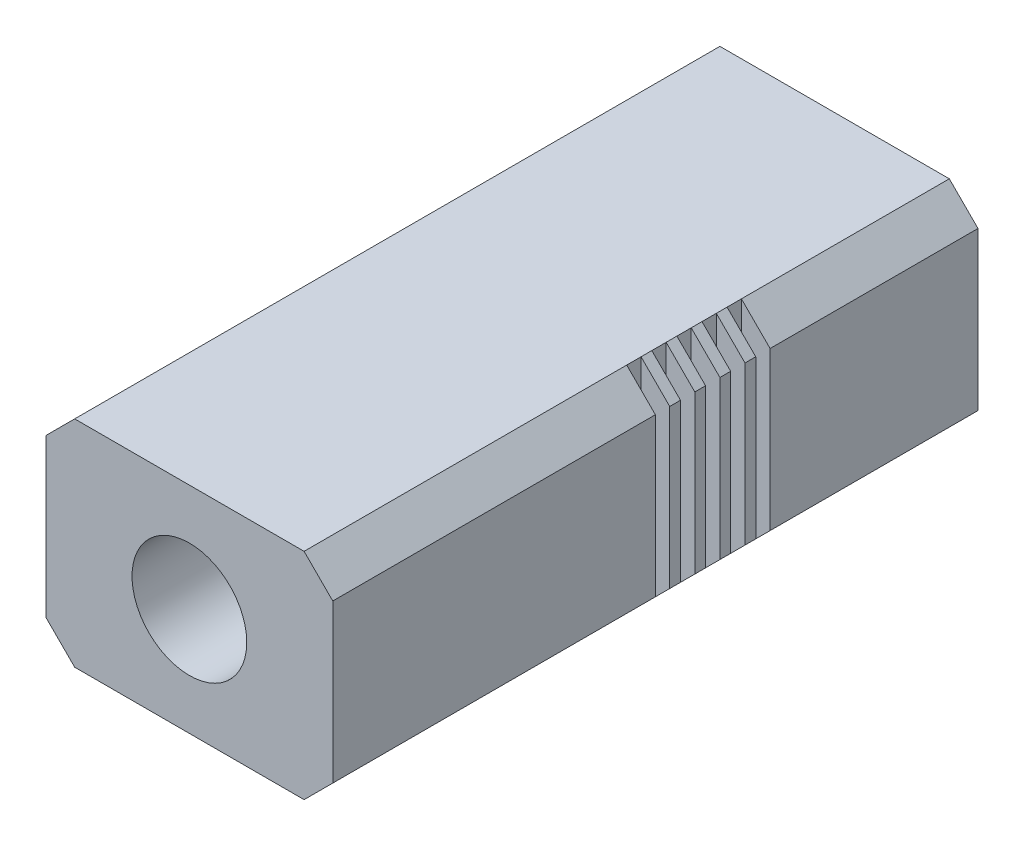
SolidWorks part; units mm, degrees
ref_plane "Front Plane" through (0, 0, 0) normal (0, 0, 1) x (1, 0, 0)
ref_plane "Top Plane" through (0, 0, 0) normal (0, 1, 0) x (1, 0, 0)
ref_plane "Right Plane" through (0, 0, 0) normal (1, 0, 0) x (0, 0, -1)
sketch "Sketch1" plane through (0, 0, 0) normal (0, 0, 1) x (1, 0, 0)
  line L0 (-10, 7.5) -> (-10, -7.5)
  line L1 (-10, 7.5) -> (10, 7.5)
  line L2 (-10, -7.5) -> (10, -7.5)
  line L3 (10, 7.5) -> (10, -7.5)
  line L4 (-10, 7.5) -> (10, -7.5) construction
  dimension "D1" = 20
  dimension "D2" = 15
extrude "Boss-Extrude1" add sketch "Sketch1" along normal blind 45
sketch "Sketch2" plane through (0, 0, 45) normal (0, 0, 1) x (1, 0, 0)
  circle A1 centre (0, 0) radius 4
  dimension "D3" = 8
extrude "Cut-Extrude1" cut sketch "Sketch2" against normal through all
chamfer "Chamfer1" distance 2 angle 45 4 edges at (-10, 7.5, 22.5) (-10, -7.5, 22.5) (10, -7.5, 22.5) (10, 7.5, 22.5)
sketch "Sketch4" plane through (0, -7.5, 0) normal (0, -1, 0) x (1, 0, 0)
  line L0 (-8, 45) -> (-8, 0) construction
  line L1 (-8, 14.5) -> (-10, 14.5)
  line L2 (-8, 14.5) -> (-8, 15.5)
  line L3 (-8, 15.5) -> (-10, 15.5)
  line L4 (-10, 14.5) -> (-10, 15.5)
  line L5 (-10, 0) -> (-10, 45) construction
  line L6 (10, 22.5) -> (-8, 22.5) construction
  line L7 (-8, 16.25) -> (-10, 16.25)
  line L8 (-8, 16.25) -> (-8, 17.25)
  line L9 (-8, 17.25) -> (-10, 17.25)
  line L10 (-10, 16.25) -> (-10, 17.25)
  line L11 (-8, 18) -> (-10, 18)
  line L12 (-8, 18) -> (-8, 19)
  line L13 (-8, 19) -> (-10, 19)
  line L14 (-10, 18) -> (-10, 19)
  line L15 (-8, 19.75) -> (-10, 19.75)
  line L16 (-8, 19.75) -> (-8, 20.75)
  line L17 (-8, 20.75) -> (-10, 20.75)
  line L18 (-10, 19.75) -> (-10, 20.75)
  line L19 (-8, 21.5) -> (-10, 21.5)
  line L20 (-8, 21.5) -> (-8, 22.5)
  line L21 (-8, 22.5) -> (-10, 22.5)
  line L22 (-10, 21.5) -> (-10, 22.5)
  line L23 (10, 45) -> (10, 0) construction
  line L24 (0, 0) -> (0, 22.5) construction
  line L25 (10, 21.5) -> (10, 22.5)
  line L26 (8, 22.5) -> (10, 22.5)
  line L27 (8, 21.5) -> (8, 22.5)
  line L28 (8, 21.5) -> (10, 21.5)
  line L29 (10, 19.75) -> (10, 20.75)
  line L30 (8, 20.75) -> (10, 20.75)
  line L31 (8, 19.75) -> (8, 20.75)
  line L32 (8, 19.75) -> (10, 19.75)
  line L33 (10, 18) -> (10, 19)
  line L34 (8, 19) -> (10, 19)
  line L35 (8, 18) -> (8, 19)
  line L36 (8, 18) -> (10, 18)
  line L37 (10, 16.25) -> (10, 17.25)
  line L38 (8, 17.25) -> (10, 17.25)
  line L39 (8, 16.25) -> (8, 17.25)
  line L40 (8, 16.25) -> (10, 16.25)
  line L41 (10, 14.5) -> (10, 15.5)
  line L42 (8, 15.5) -> (10, 15.5)
  line L43 (8, 14.5) -> (8, 15.5)
  line L44 (8, 14.5) -> (10, 14.5)
  dimension "D2" = 1
  dimension "D4" = 0.75
  dimension "D3" = 5
extrude "Cut-Extrude2" cut sketch "Sketch4" against normal through all
sketch "Sketch5" plane through (0, -7.5, 0) normal (0, -1, 0) x (1, 0, 0)
  line L0 (-2, 16) -> (-2, 8)
  line L1 (-2, 16) -> (2, 16)
  line L2 (-2, 8) -> (2, 8)
  line L3 (2, 16) -> (2, 8)
  line L4 (0, 8) -> (0, 0) construction
  line L5 (0, 16) -> (0, 11) construction
  circle A0 centre (0, 11) radius 1.25
  dimension "D3" = 2.5
  dimension "D4" = 5
  dimension "D1" = 4
  dimension "D2" = 8
  dimension "D5" = 8
extrude "Cut-Extrude3" cut sketch "Sketch5" against normal blind 1
